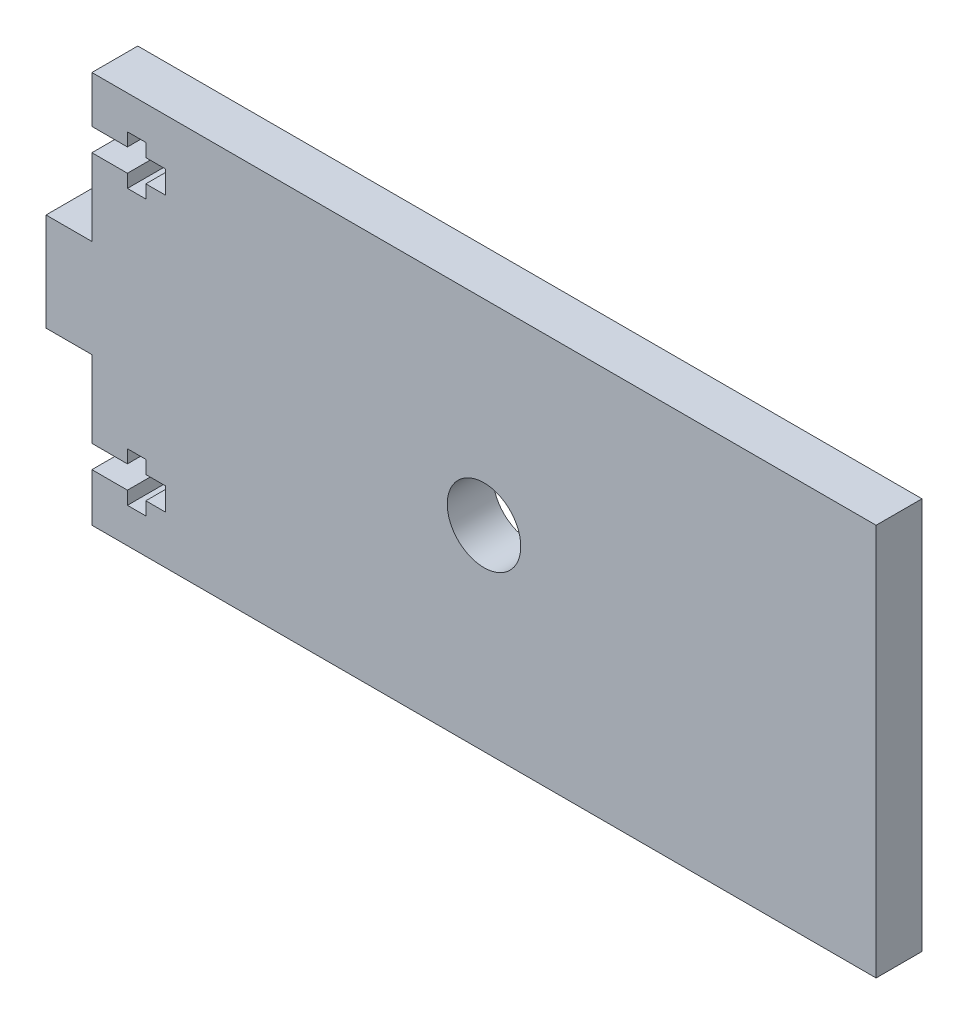
SolidWorks part; units mm, degrees
ref_plane "Front Plane" through (0, 0, 0) normal (0, 0, 1) x (1, 0, 0)
ref_plane "Top Plane" through (0, 0, 0) normal (0, 1, 0) x (1, 0, 0)
ref_plane "Right Plane" through (0, 0, 0) normal (1, 0, 0) x (0, 0, -1)
sketch "Sketch1" plane through (0, 0, 0) normal (0, 0, 1) x (1, 0, 0)
  line L1 (0, 0) -> (101.6, 0)
  line L2 (0, 0) -> (0, 50.8)
  line L3 (0, 50.8) -> (101.6, 50.8)
  line L4 (101.6, 0) -> (101.6, 50.8)
  dimension "D1" = 101.6
  dimension "D2" = 50.8
extrude "Boss-Extrude1" add sketch "Sketch1" along normal blind 5.9436
sketch "Sketch2" plane through (0, 0, 5.9436) normal (0, 0, 1) x (1, 0, 0)
  line L0 (0, 25.4) -> (101.6, 25.4) construction
  line L1 (0, 50.8) -> (0, 0) construction
  line L2 (101.6, 0) -> (101.6, 50.8) construction
  circle A0 centre (50.8, 25.4) radius 4.7625
  dimension "D1" = 9.525
  dimension "D2" = 50.8
extrude "Cut-Extrude1" cut sketch "Sketch2" against normal through all
sketch "Sketch3" plane through (0, 0, 0) normal (0, 0, -1) x (-1, 0, 0)
  line L0 (0, 19.1421) -> (5.9433, 19.1421)
  line L1 (0, 50.8) -> (0, 0) construction
  line L2 (5.9433, 19.1421) -> (-0.0003, 19.1421) construction
  line L3 (5.9433, 19.1421) -> (5.9433, 31.8421)
  line L4 (5.9433, 31.8421) -> (0, 31.8421)
  line L5 (-0.0003, 31.8421) -> (5.9433, 31.8421) construction
  line L6 (0, 31.8421) -> (0, 19.1421)
extrude "Boss-Extrude2" add sketch "Sketch3" against normal up to surface (5.9436 mm away) up to face at (55.5625, 25.4, 5.9436)
sketch "Sketch5" plane through (0, 0, 0) normal (0, 0, -1) x (-1, 0, 0)
  line L1 (0, 41.7989) -> (-4.604, 41.7989)
  line L12 (0, 50.8) -> (0, 31.8421) construction
  line L26 (-0.0003, 41.7989) -> (-4.604, 41.7989) construction
  line L27 (-4.604, 41.7989) -> (-4.604, 40.0971)
  line L28 (-4.604, 40.0971) -> (-6.9853, 40.0971)
  line L29 (-6.9853, 40.0971) -> (-6.9853, 41.7989)
  line L30 (-6.9853, 41.7989) -> (-9.5253, 41.7989)
  line L31 (-9.5253, 41.7989) -> (-9.5253, 44.7453)
  line L32 (-9.5253, 44.7453) -> (-6.9853, 44.7453)
  line L33 (-6.9853, 44.7453) -> (-6.9853, 46.4471)
  line L34 (-6.9853, 46.4471) -> (-4.604, 46.4471)
  line L35 (-4.604, 46.4471) -> (-4.604, 44.7453)
  line L36 (-4.604, 44.7453) -> (0, 44.7453)
  line L37 (-4.604, 44.7453) -> (-0.0003, 44.7453) construction
  line L39 (5.9433, 25.4921) -> (-15.3214, 25.4921) construction
  line L40 (5.9433, 31.8421) -> (5.9433, 19.1421) construction
  line L41 (-4.604, 4.5371) -> (-4.604, 6.2389)
  line L42 (-6.9853, 4.5371) -> (-4.604, 4.5371)
  line L43 (-6.9853, 6.2389) -> (-6.9853, 4.5371)
  line L44 (-4.604, 6.2389) -> (0, 6.2389)
  line L45 (-9.5253, 6.2389) -> (-6.9853, 6.2389)
  line L46 (-9.5253, 9.1853) -> (-9.5253, 6.2389)
  line L47 (-6.9853, 9.1853) -> (-9.5253, 9.1853)
  line L48 (-6.9853, 10.8871) -> (-6.9853, 9.1853)
  line L49 (-4.604, 10.8871) -> (-6.9853, 10.8871)
  line L50 (-4.604, 9.1853) -> (-4.604, 10.8871)
  line L51 (0, 9.1853) -> (-4.604, 9.1853)
  line L52 (0, 44.7453) -> (0, 41.7989)
  line L53 (0, 9.1853) -> (0, 6.2389)
extrude "Cut-Extrude2" cut sketch "Sketch5" against normal through all
